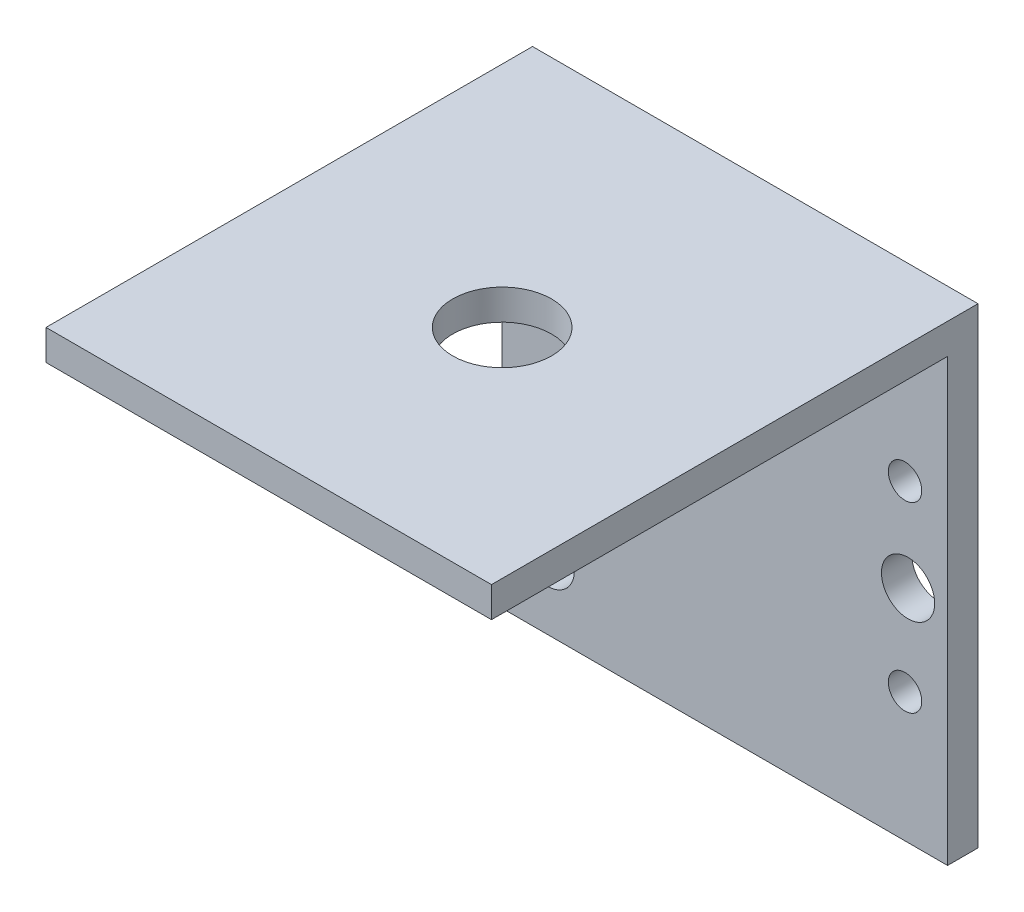
SolidWorks part; units mm, degrees
ref_plane "前视基准面" through (0, 0, 0) normal (0, 0, 1) x (1, 0, 0)
ref_plane "上视基准面" through (0, 0, 0) normal (0, 1, 0) x (1, 0, 0)
ref_plane "右视基准面" through (0, 0, 0) normal (1, 0, 0) x (0, 0, -1)
sketch "草图1" plane through (0, 0, 0) normal (0, 0, 1) x (1, 0, 0)
  line L1 (-14.65, 14.5) -> (14.65, 14.5)
  line L2 (-14.65, 14.5) -> (-14.65, -14.5)
  line L3 (-14.65, -14.5) -> (14.65, -14.5)
  line L4 (14.65, 14.5) -> (14.65, -14.5)
  line L5 (-14.65, 14.5) -> (14.65, -14.5) construction
  line L6 (-14.65, -14.5) -> (14.65, 14.5) construction
  point P0 (0, 0)
  dimension "D1" = 29
  dimension "D2" = 29.3
extrude "凸台-拉伸1" add sketch "草图1" along normal blind 2
sketch "草图2" plane through (0, 0, 2) normal (0, 0, 1) x (1, 0, 0)
  line L0 (14.65, 14.5) -> (-14.65, 14.5) construction
  line L1 (-14.65, 14.5) -> (-14.65, -14.5) construction
  circle A0 centre (-11.65, 10) radius 1.75
  circle A1 centre (-11.65, -10) radius 1.75
  circle A2 centre (12.05, 0) radius 1.75
  point P8 (-10.0659, 10)
  point P9 (-9.046, 10)
  point P10 (0, 0)
  point P11 (12.4578, 0)
  point P14 (12.05, 0)
  point P15 (0, 0)
  dimension "D1" = 3.5
  dimension "D2" = 3.5
  dimension "D3" = 3.5
  dimension "D4" = 20
  dimension "D6" = 23.7
  dimension "D5" = 4.5
  dimension "D7" = 3
extrude "切除-拉伸1" cut sketch "草图2" against normal blind 2
sketch "草图3" plane through (0, 0, 2) normal (0, 0, 1) x (1, 0, 0)
  line L0 (-14.65, 14.5) -> (-14.65, -14.5) construction
  line L1 (14.65, 14.5) -> (-14.65, 14.5) construction
  circle A0 centre (-10.15, 5.9952) radius 1.1
  circle A1 centre (-10.15, -6.0048) radius 1.1
  circle A2 centre (11.85, 5.9952) radius 1.1
  circle A3 centre (11.85, -6.0048) radius 1.1
  point P8 (0, 0)
  point P9 (0, 0)
  point P12 (0, 0)
  point P13 (0, 0)
  point P14 (0, 0)
  point P15 (11.85, -6.0048)
  dimension "D1" = 2.2
  dimension "D2" = 2.2
  dimension "D3" = 2.2
  dimension "D4" = 2.2
  dimension "D5" = 12
  dimension "D8" = 8.5048
  dimension "D6" = 4.5
  dimension "D7" = 22
extrude "切除-拉伸2" cut sketch "草图3" against normal blind 2
sketch "草图4" plane through (0, 0, 2) normal (0, 0, 1) x (1, 0, 0)
  line L1 (-14.65, 14.5) -> (14.65, 14.5)
  line L2 (-14.65, 14.5) -> (-14.65, 16.5)
  line L3 (-14.65, 16.5) -> (14.65, 16.5)
  line L4 (14.65, 14.5) -> (14.65, 16.5)
  dimension "D1" = 29.3
  dimension "D2" = 2
extrude "凸台-拉伸2" add sketch "草图4" along normal blind 30 and the other way blind 2
sketch "草图5" plane through (0, 14.5, 0) normal (0, -1, 0) x (1, 0, 0)
  line L0 (14.65, 2) -> (-14.65, 2) construction
  line L1 (-14.65, 2) -> (-14.65, 32) construction
  circle A0 centre (0.35, 17) radius 3.25
  dimension "D1" = 6.5
  dimension "D3" = 15
  dimension "D2" = 15
extrude "切除-拉伸3" cut sketch "草图5" against normal blind 30
